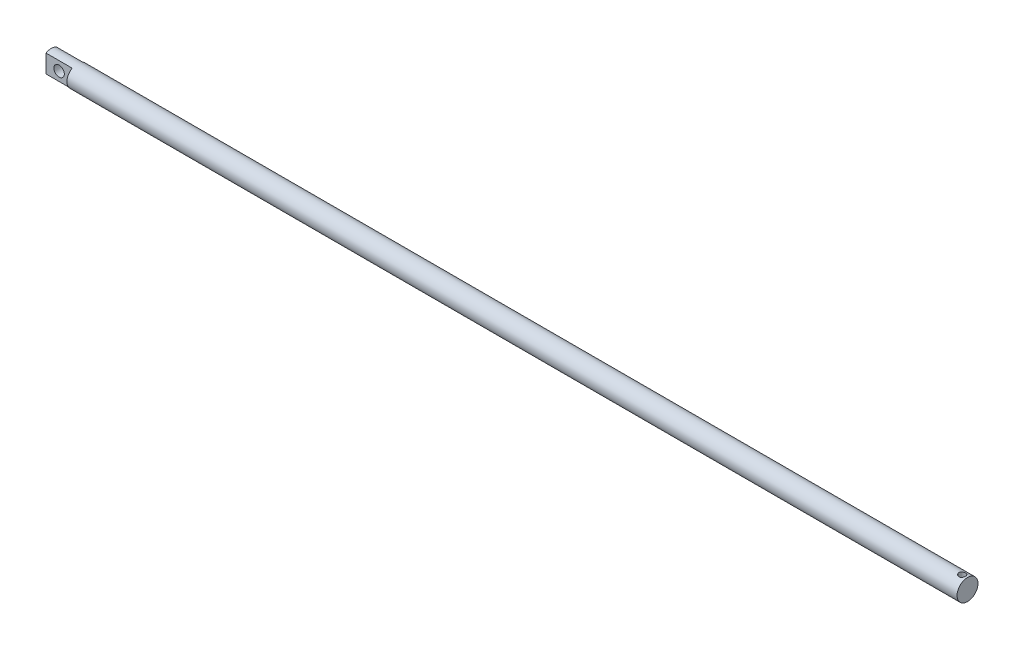
SolidWorks part; units mm, degrees
material "普通碳钢"
ref_plane "前视基准面" through (0, 0, 0) normal (0, 0, 1) x (1, 0, 0)
ref_plane "上视基准面" through (0, 0, 0) normal (0, 1, 0) x (1, 0, 0)
ref_plane "右视基准面" through (0, 0, 0) normal (1, 0, 0) x (0, 0, -1)
sketch "草图1" plane through (0, 0, 0) normal (1, 0, 0) x (0, 0, -1)
  circle A0 centre (0, 0) radius 8
  dimension "D1" = 16
extrude "凸台-拉伸1" add sketch "草图1" along normal blind 700 contours A0
sketch "草图2" plane through (0, 0, 0) normal (0, 0, 1) x (1, 0, 0)
  line L0 (0, 8) -> (0, -8) construction
  line L2 (0, 0) -> (22.073, 0) construction
  circle A0 centre (10, 0) radius 4
  dimension "D1" = 8
  dimension "D3" = 10
extrude "切除-拉伸1" cut sketch "草图2" against normal through all and the other way through all
sketch "草图3" plane through (0, 0, 0) normal (-1, 0, 0) x (0, 0, 1)
  line L0 (-4, 10) -> (-4, -10)
  line L1 (-4, 10) -> (4, 10)
  line L2 (4, 10) -> (4, -10)
  line L3 (-4, -10) -> (4, -10)
  dimension "D1" = 4
  dimension "D2" = 4
  dimension "D3" = 20
  dimension "D4" = 10
extrude "切除-拉伸2" cut sketch "草图3" against normal blind 20 flip side to cut
sketch "草图4" plane through (0, 0, 0) normal (0, 1, 0) x (1, 0, 0)
  line L0 (696, 0) -> (700, 0) construction
  line L1 (700, -8) -> (700, 8) construction
  circle A0 centre (696, 0) radius 2.5
  dimension "D1" = 5
  dimension "D2" = 4
extrude "切除-拉伸3" cut sketch "草图4" against normal mid plane 20
